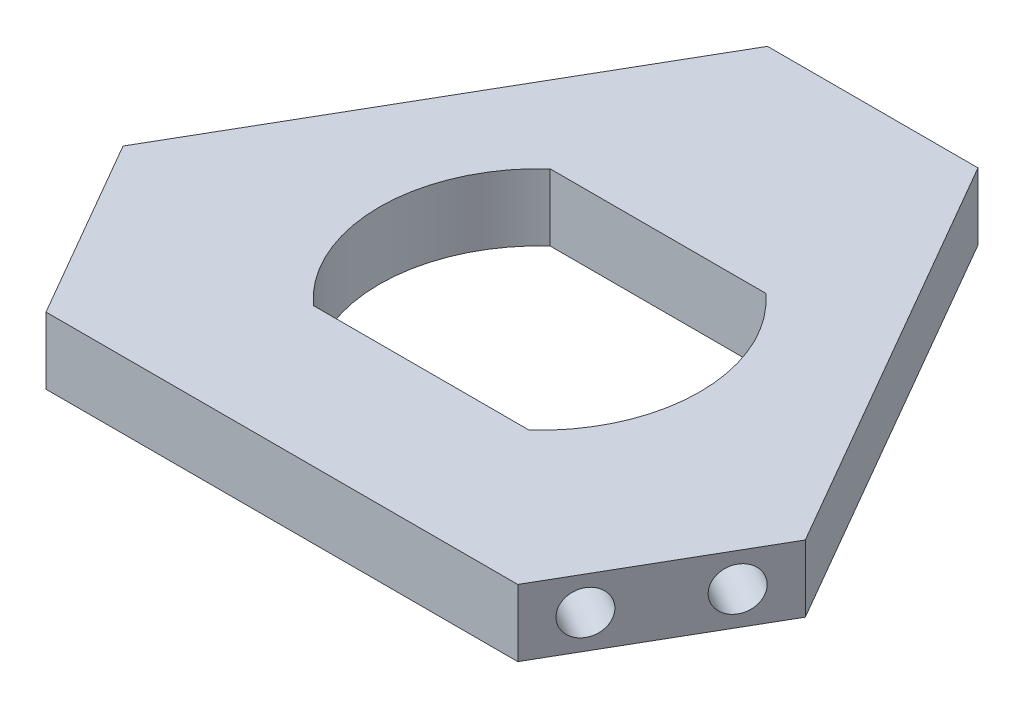
SolidWorks part; units mm, degrees
ref_plane "Alzado" through (0, 0, 0) normal (0, 0, 1) x (1, 0, 0)
ref_plane "Planta" through (0, 0, 0) normal (0, 1, 0) x (1, 0, 0)
ref_plane "Vista lateral" through (0, 0, 0) normal (1, 0, 0) x (0, 0, -1)
sketch "Croquis1" plane through (0, 0, 0) normal (0, 1, 0) x (1, 0, 0)
  line L0 (0, 0) -> (0, 92.5) construction
  line L1 (16, 64.7872) -> (-16, 64.7872) construction
  line L2 (0, 92.5) -> (-80.1073, -46.25) construction
  line L3 (-80.1073, -46.25) -> (80.1073, -46.25) construction
  line L4 (80.1073, -46.25) -> (0, 92.5) construction
  line L5 (-16, 64.7872) -> (-64.1073, -18.5372) construction
  line L6 (-64.1073, -18.5372) -> (-48.1073, -46.25) construction
  line L7 (-48.1073, -46.25) -> (48.1073, -46.25) construction
  line L8 (64.1073, -18.5372) -> (48.1073, -46.25) construction
  line L9 (16, 64.7872) -> (64.1073, -18.5372) construction
  line L10 (0, 0) -> (59.8573, -25.8984) construction
  line L11 (-28.75, 21.25) -> (28.75, 21.25)
  line L12 (-28.75, 21.25) -> (-28.75, -21.25)
  line L13 (-28.75, -21.25) -> (28.75, -21.25)
  line L14 (28.75, 21.25) -> (28.75, -21.25)
  line L15 (-28.75, 21.25) -> (28.75, -21.25) construction
  line L16 (-28.75, -21.25) -> (28.75, 21.25) construction
  line L17 (59.8573, -25.8984) -> (52.3573, -38.8888) construction
  line L18 (52.3573, -38.8888) -> (0, 0) construction
  line L19 (56.1073, -32.3936) -> (0, 0) construction
  line L20 (0, 0) -> (46.25, 0) construction
  line L21 (-48.1073, -46.25) -> (0, -46.25) construction
  line L24 (0, -46.25) -> (48.1073, -46.25) construction
  line L25 (-18.8868, 59.7872) -> (-61.2206, -13.5372)
  line L26 (-61.2206, -13.5372) -> (-42.3338, -46.25)
  line L27 (-42.3338, -46.25) -> (42.3338, -46.25)
  line L28 (42.3338, -46.25) -> (61.2206, -13.5372)
  line L29 (61.2206, -13.5372) -> (18.8868, 59.7872)
  line L30 (18.8868, 59.7872) -> (-18.8868, 59.7872)
  circle A0 centre (0, 0) radius 92.5 construction
  circle A1 centre (0, 0) radius 46.25 construction
  circle A2 centre (0, 0) radius 5 construction
  point P15 (0, -46.25)
  point P17 (0, 64.7872)
  dimension "D1" = 185
  dimension "D5" = 10
  dimension "D2" = 120
  dimension "D3" = 16
  dimension "D4" = 32
  dimension "D6" = 57.5
  dimension "D7" = 42.5
  dimension "D8" = 15
  dimension "D9" = 13.207
  dimension "D10" = 5
extrude "Saliente-Extruir1" add sketch "Croquis1" along normal blind 12
sketch "Croquis7" plane through (0, 0, 0) normal (0, 1, 0) x (1, 0, 0)
  line L0 (28.75, 21.25) -> (28.75, -21.25) construction
  line L1 (16, 64.7872) -> (64.1073, -18.5372) construction
  circle A0 centre (0, 0) radius 28.75
  circle A1 centre (0, 0) radius 46.25
extrude "Saliente-Extruir2" add sketch "Croquis7" along normal blind 12
sketch "Croquis8" plane through (51.7772, 0, 29.8936) normal (0.866, 0, 0.5) x (0.5, 0, -0.866)
  line L0 (-10, 6) -> (10, 6) construction
  line L1 (-18.8868, 0) -> (18.8868, 0) construction
  line L2 (0, 6) -> (0, 0) construction
  circle A0 centre (-10, 6) radius 3.875
  circle A1 centre (10, 6) radius 3.875
  dimension "D1" = 7.75
  dimension "D2" = 6
  dimension "D3" = 20
extrude "Cortar-Extruir1" cut sketch "Croquis8" against normal blind 10
pattern_circular "MatrizC1" count 3 every 120 about axis through (0, 0, 0) along (0, 1, 0) of "Cortar-Extruir1"
